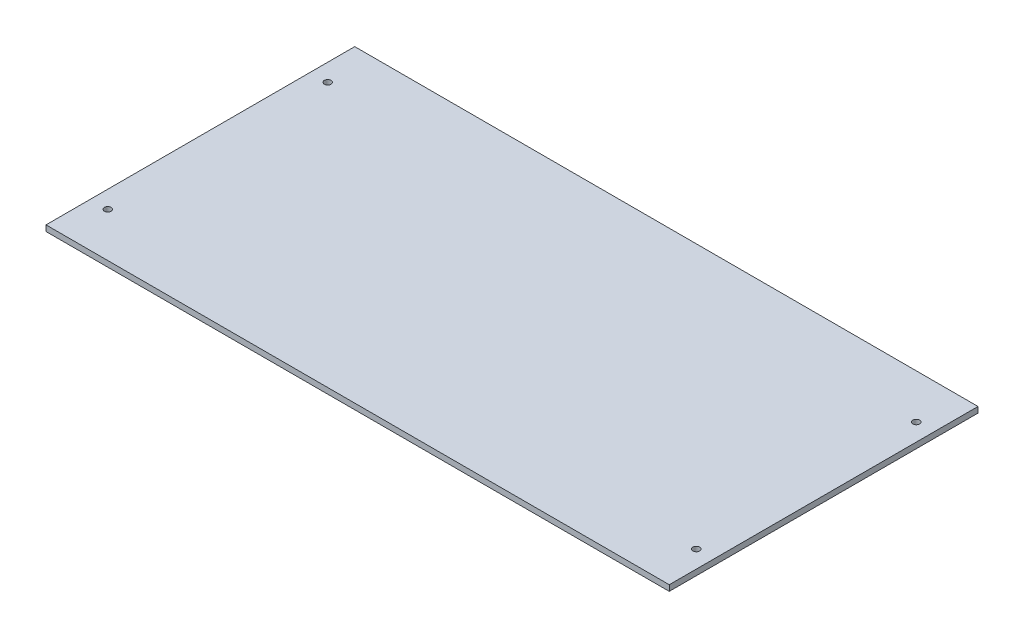
SolidWorks part; units mm, degrees
material "Acrylic (Medium-high impact)"
ref_plane "Front Plane" through (0, 0, 0) normal (0, 0, 1) x (1, 0, 0)
ref_plane "Top Plane" through (0, 0, 0) normal (0, 1, 0) x (1, 0, 0)
ref_plane "Right Plane" through (0, 0, 0) normal (1, 0, 0) x (0, 0, -1)
sketch "Sketch1" plane through (0, 0, 0) normal (0, 1, 0) x (1, 0, 0)
  line L1 (-161.5, 80) -> (161.5, 80)
  line L2 (-161.5, 80) -> (-161.5, -80)
  line L3 (-161.5, -80) -> (161.5, -80)
  line L4 (161.5, 80) -> (161.5, -80)
  line L5 (-161.5, 80) -> (161.5, -80) construction
  line L6 (-161.5, -80) -> (161.5, 80) construction
  point P0 (0, 0)
  dimension "D1" = 160
  dimension "D2" = 323
extrude "Boss-Extrude1" add sketch "Sketch1" along normal blind 3
sketch "Sketch2" plane through (0, 0, 0) normal (0, -1, 0) x (1, 0, 0)
  line L0 (161.5, -80) -> (-161.5, -80) construction
  line L1 (-161.5, -80) -> (-161.5, 80) construction
  line L2 (161.5, 80) -> (161.5, -80) construction
  line L3 (-161.5, 0) -> (161.5, 0) construction
  line L7 (161.5, -80) -> (161.5, 80)
  line L8 (161.5, 80) -> (-161.5, 80)
  line L9 (-161.5, 80) -> (-161.5, -80)
  line L10 (-161.5, -80) -> (161.5, -80)
  line L11 (161.5, -80) -> (161.5, 80) construction
  line L12 (161.5, 80) -> (-161.5, 80) construction
  line L13 (-161.5, 80) -> (-161.5, -80) construction
  line L14 (-161.5, -80) -> (161.5, -80) construction
  circle A0 centre (-152.5, -57) radius 1.75
  circle A1 centre (152.5, -57) radius 1.75
  circle A2 centre (152.5, 57) radius 1.75
  circle A3 centre (-152.5, 57) radius 1.75
  dimension "D1" = 3.5
  dimension "D4" = 3.5
  dimension "D2" = 23
  dimension "D3" = 9
  dimension "D5" = 23
  dimension "D6" = 9
  dimension "D7" = 0
extrude "Cut-Extrude1" cut sketch "Sketch2" against normal through all
